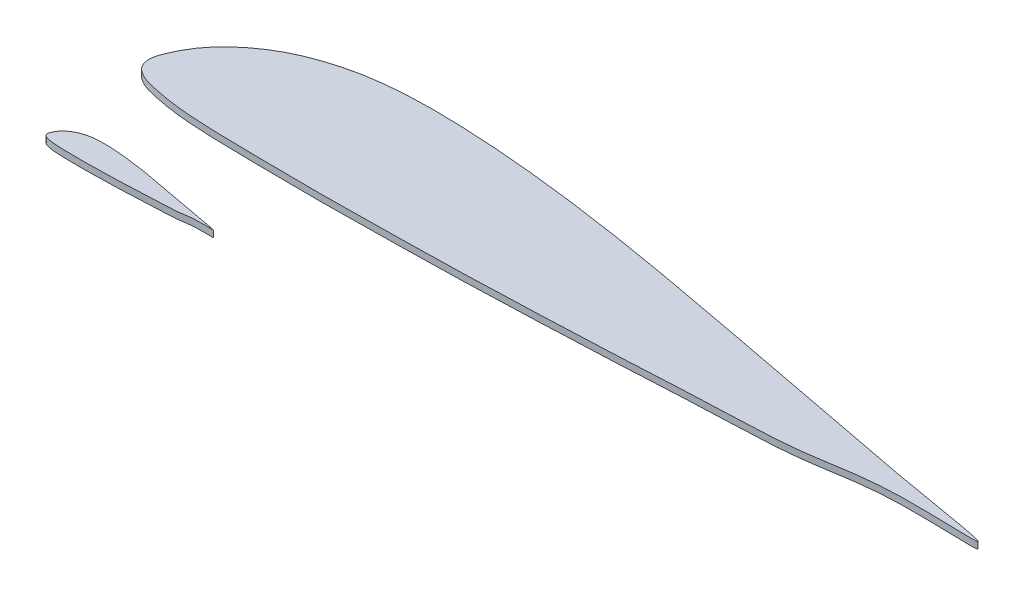
SolidWorks part; units mm, degrees
ref_plane "Front Plane" through (0, 0, 0) normal (0, 0, 1) x (1, 0, 0)
ref_plane "Top Plane" through (0, 0, 0) normal (0, 1, 0) x (1, 0, 0)
ref_plane "Right Plane" through (0, 0, 0) normal (1, 0, 0) x (0, 0, -1)
sketch "Sketch2" plane through (0, 0, 0) normal (0, 1, 0) x (1, 0, 0)
  line L0 (0, 0) -> (100, 0) construction
  spline S0 degree 3 poles (88.4175, 0.541) (105.7801, -0.646) (88.4238, 2.0772) (80.4225, 3.7533) (69.8862, 5.7094) (60.0387, 7.6078) (50.0167, 9.4488) (40.0326, 10.974) (31.6814, 11.8576) (25.0037, 12.2188) (19.9913, 12.2559) (14.932, 11.8315) (10.5527, 10.7172) (7.226, 9.2643) (4.8941, 7.7409) (3.2273, 6.3021) (1.9076, 4.7846) (1.0905, 3.5176) (0.3111, 1.9497) (-0.2747, 0.388) (0.3224, -0.986) (1.1281, -1.5533) (1.9607, -1.9804) (3.3251, -2.3144) (4.9885, -2.6515) (7.3259, -2.9608) (10.6627, -3.1833) (14.9997, -3.2523) (19.9997, -3.318) (25.0003, -3.3357) (31.6666, -3.2336) (40.0045, -3.1188) (49.9937, -2.7479) (60.0321, -2.3291) (69.8873, -1.7353) (80.4502, -1.5289) (88.4175, 0.541) (105.7801, -0.646) (88.4238, 2.0772) knots -0.144975 -0.096715 -0.048179 0 0.049041 0.098082 0.147123 0.196163 0.245117 0.293835 0.342264 0.366386 0.390475 0.414675 0.439566 0.455415 0.466908 0.479712 0.48709 0.495937 0.501323 0.512663 0.51831 0.521365 0.526752 0.531755 0.541582 0.551305 0.565797 0.589895 0.613986 0.638076 0.662167 0.710354 0.75856 0.806786 0.855025 0.903285 0.951821 1 1.049041 1.098082 1.147123 only from (100, 0) to (100, 0)
  spline S1 degree 3 poles (434.0873, 70.357) (520.9004, 64.4222) (434.1189, 78.038) (394.1126, 86.4188) (341.4309, 96.1993) (292.1933, 105.6909) (242.0837, 114.8961) (192.1632, 122.5222) (150.4072, 126.9402) (117.0187, 128.7461) (91.9564, 128.9316) (66.6601, 126.8097) (44.7635, 121.2381) (28.1301, 113.9735) (16.4707, 106.3566) (8.1366, 99.1625) (1.5379, 91.575) (-2.5474, 85.2401) (-6.4445, 77.4008) (-9.3735, 69.5919) (-6.3879, 62.7222) (-2.3596, 59.8857) (1.8037, 57.7501) (8.6254, 56.0801) (16.9424, 54.3945) (28.6295, 52.848) (45.3135, 51.7356) (66.9987, 51.3906) (91.9985, 51.0622) (117.0015, 50.9735) (150.3331, 51.484) (192.0227, 52.0581) (241.9685, 53.9125) (292.1604, 56.0067) (341.4363, 58.9756) (394.2509, 60.0076) (434.0873, 70.357) (520.9004, 64.4222) (434.1189, 78.038) knots -0.144975 -0.096715 -0.048179 0 0.049041 0.098082 0.147123 0.196163 0.245117 0.293835 0.342264 0.366386 0.390475 0.414675 0.439566 0.455415 0.466908 0.479712 0.48709 0.495937 0.501323 0.512663 0.51831 0.521365 0.526752 0.531755 0.541582 0.551305 0.565797 0.589895 0.613986 0.638076 0.662167 0.710354 0.75856 0.806786 0.855025 0.903285 0.951821 1 1.049041 1.098082 1.147123 only from (492, 67.6521) to (492, 67.6521)
  point P3 (0.5, 2.3)
  point P4 (1, 3.3)
  point P5 (2, 4.84)
  point P6 (3, 6)
  point P7 (5, 7.75)
  point P8 (7, 9.05)
  point P9 (10, 10.4)
  point P10 (15, 11.7)
  point P11 (20, 12.18)
  point P12 (25, 12.18)
  point P13 (30, 11.92)
  point P14 (40, 10.9)
  point P15 (60, -2.3)
  point P16 (50, -2.74)
  point P17 (40, -3.08)
  point P18 (30, -3.26)
  point P19 (25, -3.32)
  point P20 (20, -3.31)
  point P21 (15, -3.25)
  point P22 (10, -3.12)
  point P23 (7, -2.9)
  point P24 (5, -2.63)
  point P25 (3, -2.23)
  point P26 (2, -1.95)
  point P27 (1, -1.45)
  point P28 (0.5, -1.06)
  point P29 (50, 9.4)
  point P30 (70, 5.7)
  point P31 (60, 7.6)
  point P32 (80, 3.8)
  point P33 (90, 1.9)
  point P34 (100, 0)
  point P35 (70, -1.8)
  point P36 (80, -1.22)
  point P37 (90, -0.0001)
  dimension "D1" = 100
  dimension "D3" = 1
  dimension "D4" = 2
  dimension "D5" = 3
  dimension "D6" = 5
  dimension "D7" = 7
  dimension "D8" = 10
  dimension "D9" = 15
  dimension "D10" = 20
  dimension "D11" = 25
  dimension "D12" = 30
  dimension "D13" = 40
  dimension "D14" = 50
  dimension "D15" = 70
  dimension "D16" = 60
  dimension "D17" = 80
  dimension "D18" = 90
  dimension "D19" = 100
  dimension "D20" = 2.3
  dimension "D21" = 3.3
  dimension "D22" = 4.84
  dimension "D23" = 6
  dimension "D24" = 7.75
  dimension "D25" = 9.05
  dimension "D26" = 10.4
  dimension "D27" = 11.7
  dimension "D28" = 12.18
  dimension "D29" = 12.18
  dimension "D30" = 11.92
  dimension "D31" = 10.9
  dimension "D32" = 9.4
  dimension "D33" = 7.6
  dimension "D34" = 5.7
  dimension "D35" = 3.8
  dimension "D36" = 1.9
  dimension "D37" = 0
  dimension "D38" = 0.5
  dimension "D39" = 1.06
  dimension "D40" = 1.45
  dimension "D41" = 1.95
  dimension "D42" = 2.23
  dimension "D43" = 2.63
  dimension "D44" = 2.9
  dimension "D45" = 3.12
  dimension "D46" = 3.25
  dimension "D47" = 3.31
  dimension "D48" = 3.32
  dimension "D49" = 3.26
  dimension "D50" = 3.08
  dimension "D51" = 2.74
  dimension "D52" = 2.3
  dimension "D53" = 1.8
  dimension "D54" = 1.22
  dimension "D55" = 0.0001
extrude "Boss-Extrude2" add sketch "Sketch2" along normal blind 4
